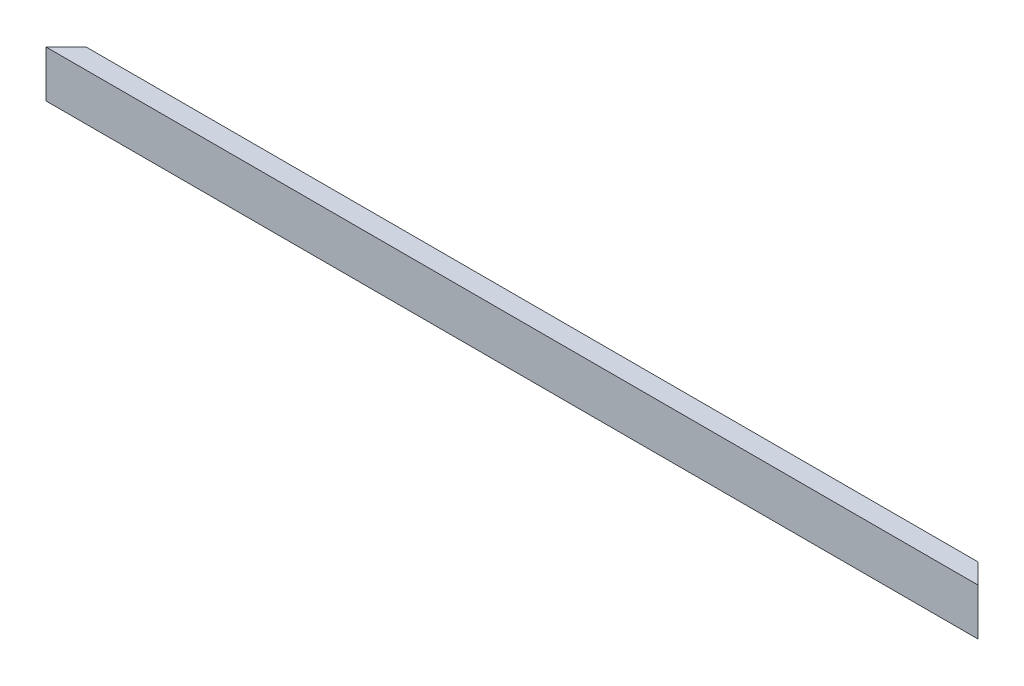
SolidWorks part; units mm, degrees
material "Pine"
ref_plane "Front Plane" through (0, 0, 0) normal (0, 0, 1) x (1, 0, 0)
ref_plane "Top Plane" through (0, 0, 0) normal (0, 1, 0) x (1, 0, 0)
ref_plane "Right Plane" through (0, 0, 0) normal (1, 0, 0) x (0, 0, -1)
sketch "Sketch1" plane through (0, 0, 0) normal (0, 1, 0) x (1, 0, 0)
  line L1 (0, 0) -> (1771.65, 0)
  line L2 (0, 0) -> (0, 38.1)
  line L3 (0, 38.1) -> (1771.65, 38.1)
  line L4 (1771.65, 0) -> (1771.65, 38.1)
  dimension "D1" = 38.1
  dimension "D2" = 1771.65
extrude "Boss-Extrude1" add sketch "Sketch1" along normal blind 88.9
sketch "Sketch2" plane through (0, 0, 0) normal (0, 1, 0) x (1, 0, 0)
  line L11 (0, 0) -> (38.1, 38.1)
  line L12 (1771.65, 38.1) -> (0, 38.1) construction
  line L13 (38.1, 38.1) -> (0, 38.1)
  line L14 (0, 38.1) -> (0, 0)
  line L15 (1771.65, 0) -> (1733.55, 38.1)
  line L16 (1733.55, 38.1) -> (1771.65, 38.1)
  line L17 (1771.65, 38.1) -> (1771.65, 0)
  dimension "D1" = 45
  dimension "D2" = 45
extrude "Cut-Extrude1" cut sketch "Sketch2" along normal through all
